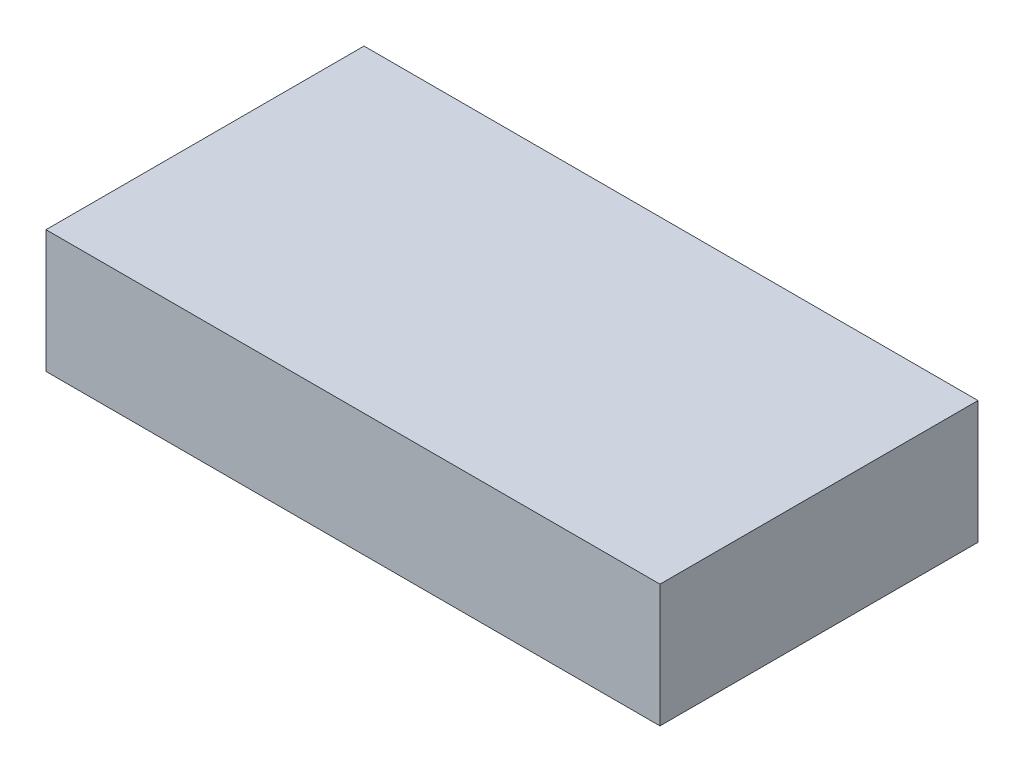
SolidWorks part; units mm, degrees
ref_plane "Front Plane" through (0, 0, 0) normal (0, 0, 1) x (1, 0, 0)
ref_plane "Top Plane" through (0, 0, 0) normal (0, 1, 0) x (1, 0, 0)
ref_plane "Right Plane" through (0, 0, 0) normal (1, 0, 0) x (0, 0, -1)
sketch "Sketch1" plane through (0, 0, 0) normal (0, 1, 0) x (1, 0, 0)
  line L1 (-74.7408, -6.7927) -> (-24.7408, -6.7927)
  line L2 (-74.7408, -6.7927) -> (-74.7408, -32.6927)
  line L3 (-74.7408, -32.6927) -> (-24.7408, -32.6927)
  line L4 (-24.7408, -6.7927) -> (-24.7408, -32.6927)
  line L5 (-74.7408, -6.7927) -> (-24.7408, -32.6927) construction
  line L6 (-74.7408, -32.6927) -> (-24.7408, -6.7927) construction
  point P0 (-49.7408, -19.7427)
  dimension "D1" = 25.9
  dimension "D2" = 50
extrude "Boss-Extrude1" add sketch "Sketch1" along normal blind 10
